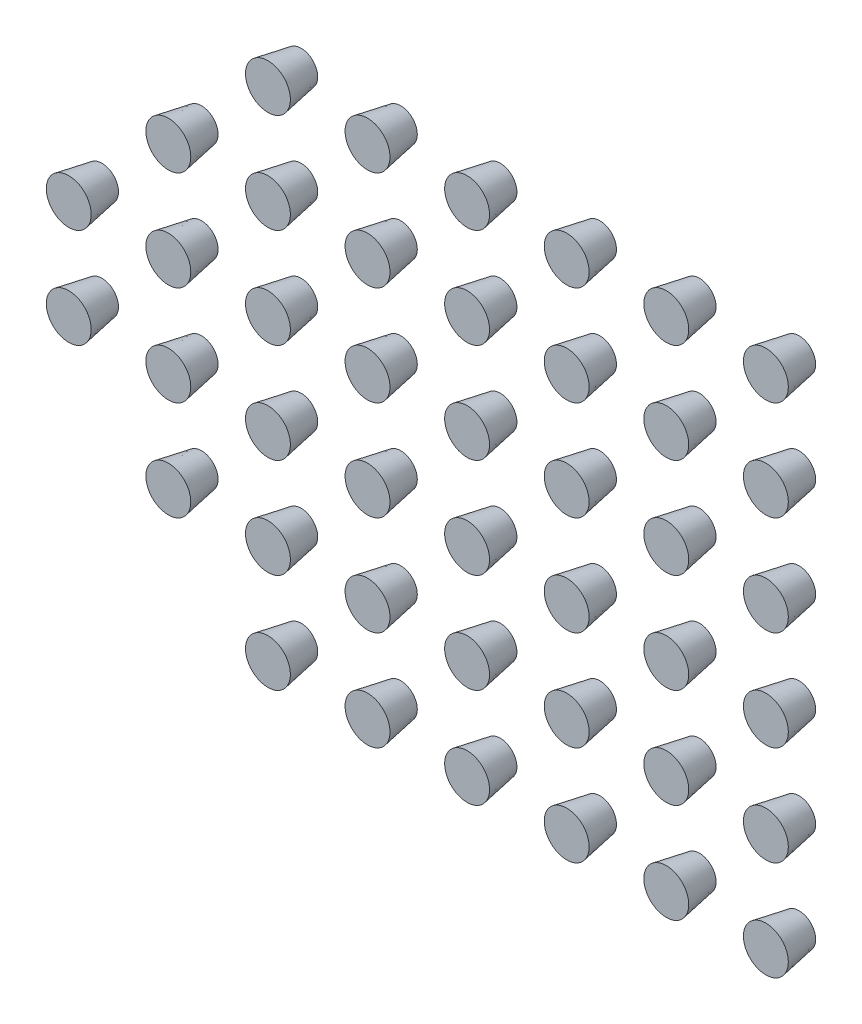
SolidWorks part; units mm, degrees
ref_plane "前视基准面" through (0, 0, 0) normal (0, 0, 1) x (1, 0, 0)
ref_plane "上视基准面" through (0, 0, 0) normal (0, 1, 0) x (1, 0, 0)
ref_plane "右视基准面" through (0, 0, 0) normal (1, 0, 0) x (0, 0, -1)
other "Configuration Table"
sketch "草图1" plane through (0, 0, 0) normal (0, 0, 1) x (1, 0, 0)
  circle A0 centre (0, 0) radius 0.5
  dimension "D1" = 1
extrude "凸台-拉伸1" add sketch "草图1" along normal blind 1 draft 10 draft outward yes
pattern_linear "阵列(线性)1" count 6 spacing 3 along (0, 1, 0) count 6 spacing 3 along (1, 0, 0) of "凸台-拉伸1"
ref_plane "基准面1" through (7.5, 0, 0) normal (1, 0, 0) x (0, 0, -1)
ref_plane "基准面2" through (0, 7.5, 0) normal (0, 1, 0) x (1, 0, 0)
pattern_linear "阵列(线性)2" count 2 spacing 3 along (-1, 0, 0) of bodies 110 109 108 107
pattern_linear "阵列(线性)3" count 2 spacing 3 along (-1, 0, 0) of bodies 143 144
